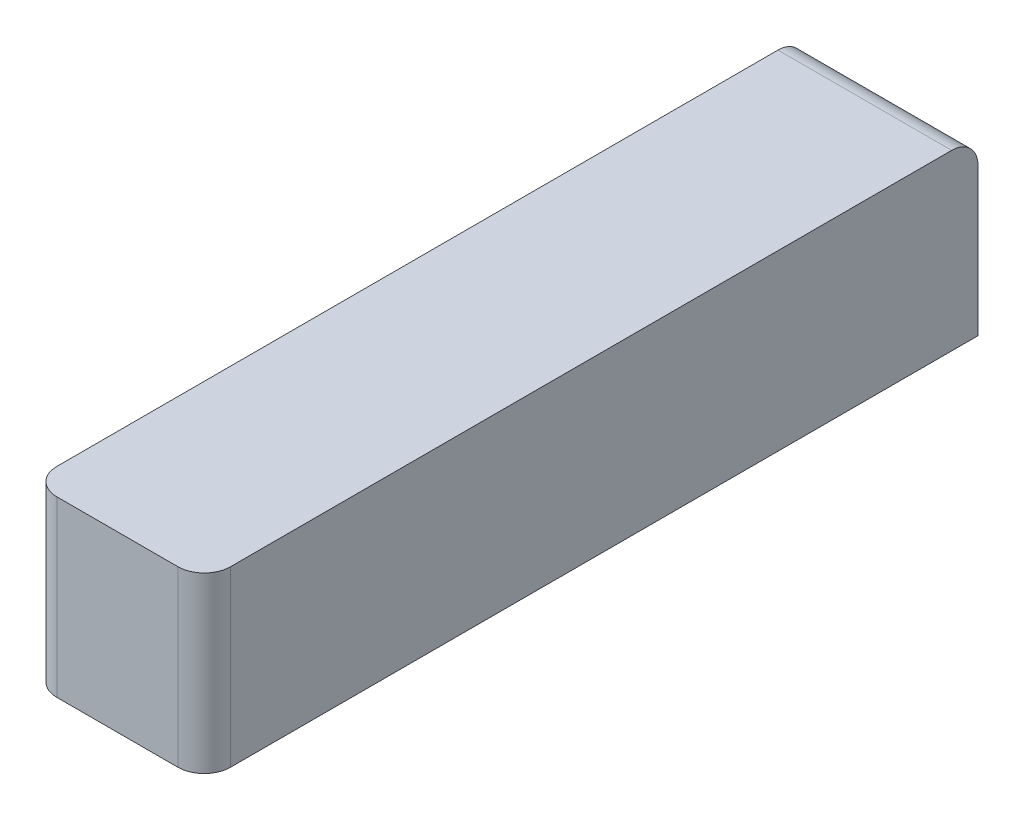
SolidWorks part; units mm, degrees
ref_plane "Front Plane" through (0, 0, 0) normal (0, 0, 1) x (1, 0, 0)
ref_plane "Top Plane" through (0, 0, 0) normal (0, 1, 0) x (1, 0, 0)
ref_plane "Right Plane" through (0, 0, 0) normal (1, 0, 0) x (0, 0, -1)
sketch "Sketch1" plane through (0, 0, 0) normal (0, 1, 0) x (1, 0, 0)
  line L1 (-16.5, -73.5) -> (16.5, -73.5)
  line L2 (-16.5, -73.5) -> (-16.5, 73.5)
  line L3 (-16.5, 73.5) -> (16.5, 73.5)
  line L4 (16.5, -73.5) -> (16.5, 73.5)
  line L5 (-16.5, -73.5) -> (16.5, 73.5) construction
  line L6 (-16.5, 73.5) -> (16.5, -73.5) construction
  point P0 (0, 0)
  dimension "D1" = 33
  dimension "D2" = 147
extrude "Boss-Extrude1" add sketch "Sketch1" along normal blind 33
fillet "Fillet1" radius 5 3 edges at (0, 33, -73.5) (-16.5, 16.5, 73.5) (16.5, 16.5, 73.5)
